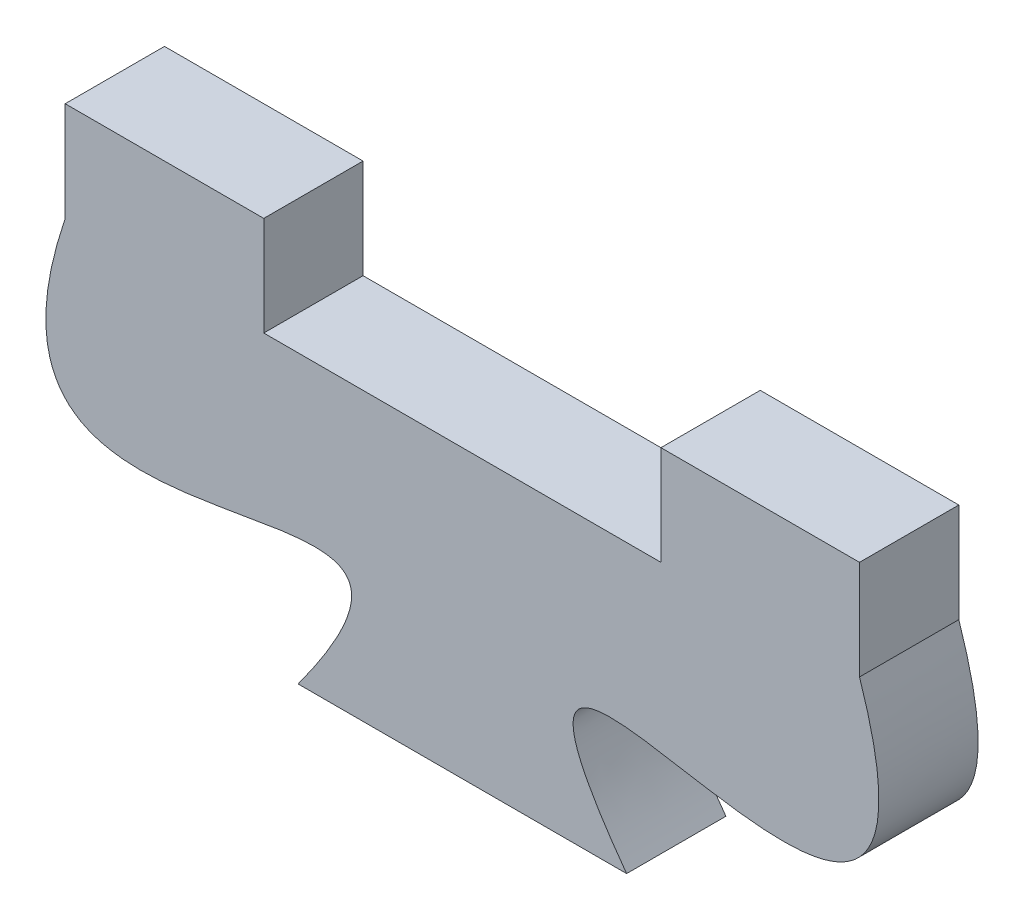
SolidWorks part; units mm, degrees
ref_plane "Front Plane" through (0, 0, 0) normal (0, 0, 1) x (1, 0, 0)
ref_plane "Top Plane" through (0, 0, 0) normal (0, 1, 0) x (1, 0, 0)
ref_plane "Right Plane" through (0, 0, 0) normal (1, 0, 0) x (0, 0, -1)
sketch "Sketch1" plane through (0, 0, 0) normal (0, 0, 1) x (1, 0, 0)
  line L0 (-66.5722, 32.1944) -> (-41.1722, 32.1944)
  line L1 (-53.8722, 32.1944) -> (-53.8722, 23.025) construction
  line L2 (-48.6197, 23.025) -> (-59.1246, 23.025)
  line L3 (-47.5222, 32.1944) -> (-47.5222, 35.3694)
  line L4 (-66.5722, 32.1944) -> (-60.2222, 32.1944)
  line L5 (-66.5722, 32.1944) -> (-66.5722, 35.3694)
  line L6 (-66.5722, 35.3694) -> (-60.2222, 35.3694)
  line L7 (-60.2222, 32.1944) -> (-60.2222, 35.3694)
  line L8 (-41.1722, 35.3694) -> (-47.5222, 35.3694)
  line L9 (-41.1722, 32.1944) -> (-41.1722, 35.3694)
  line L10 (-41.1722, 32.1944) -> (-47.5222, 32.1944)
  spline S0 degree 3 poles (-66.5722, 32.1944) (-70.7961, 19.6102) (-51.7665, 33.1167) (-59.1246, 23.025) knots 0 0 0 0 1 1 1 1
  spline S1 degree 3 poles (-41.1722, 32.1944) (-36.9482, 19.6102) (-55.9778, 33.1167) (-48.6197, 23.025) knots 0 0 0 0 1 1 1 1
  dimension "D1" = 25.4
  dimension "D2" = 9.1694
  dimension "D3" = 6.35
  dimension "D4" = 3.175
extrude "Boss-Extrude1" add sketch "Sketch1" along normal blind 3.175 contours L0 L7 L6 L5 | L1 L0 S0 L2 | L0 L1 L2 S1 | L0 L9 L8 L3
